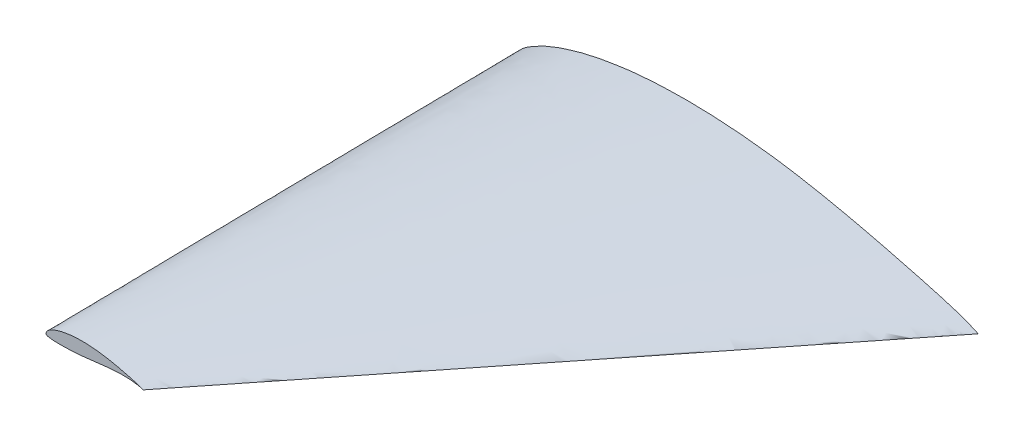
SolidWorks part; units mm, degrees
ref_plane "Front Plane" through (0, 0, 0) normal (0, 0, 1) x (1, 0, 0)
ref_plane "Top Plane" through (0, 0, 0) normal (0, 1, 0) x (1, 0, 0)
ref_plane "Right Plane" through (0, 0, 0) normal (1, 0, 0) x (0, 0, -1)
curve "Curve1"
  spline degree 3 poles (25.3433, 0.0232, 0) (25.4148, -0.0081, 0) (25.3447, 0.0413, 0) (25.2813, 0.0657, 0) (25.1364, 0.1389, 0) (24.9522, 0.2143, 0) (24.7099, 0.3099, 0) (24.4182, 0.4134, 0) (24.075, 0.5249, 0) (23.6837, 0.6446, 0) (23.2451, 0.7712, 0) (22.762, 0.9075, 0) (22.2348, 1.0483, 0) (21.6683, 1.2014, 0) (21.0618, 1.3547, 0) (20.4213, 1.5189, 0) (19.7455, 1.6791, 0) (19.0423, 1.8522, 0) (18.309, 2.0141, 0) (17.5552, 2.1876, 0) (16.7767, 2.3381, 0) (15.9845, 2.4962, 0) (15.1746, 2.6242, 0) (14.3573, 2.7555, 0) (13.5297, 2.8496, 0) (12.7014, 2.9475, 0) (11.8708, 3.0047, 0) (11.0455, 3.0663, 0) (10.2259, 3.0812, 0) (9.4176, 3.1048, 0) (8.6235, 3.079, 0) (7.8457, 3.0638, 0) (7.0909, 2.9938, 0) (6.3564, 2.9377, 0) (5.6543, 2.8235, 0) (4.9756, 2.731, 0) (4.3385, 2.581, 0) (3.7264, 2.4576, 0) (3.1656, 2.2763, 0) (2.6301, 2.1267, 0) (2.1563, 1.9205, 0) (1.705, 1.7526, 0) (1.3258, 1.5314, 0) (0.9764, 1.3443, 0) (0.6751, 1.1512, 0) (0.4363, 0.9319, 0) (0.2358, 0.7054, 0) (0.1108, 0.4617, 0) (0.0257, 0.2336, 0) (-0.0273, 0.0509, 0) (0.0322, -0.0775, 0) (0.1239, -0.1549, 0) (0.243, -0.2723, 0) (0.4522, -0.3184, 0) (0.6848, -0.4066, 0) (0.9848, -0.4273, 0) (1.3238, -0.4905, 0) (1.7178, -0.5018, 0) (2.1546, -0.5475, 0) (2.639, -0.5497, 0) (3.165, -0.58, 0) (3.7327, -0.5712, 0) (4.3384, -0.5844, 0) (4.9797, -0.5607, 0) (5.6547, -0.5539, 0) (6.359, -0.5141, 0) (7.0916, -0.4857, 0) (7.8469, -0.4269, 0) (8.6243, -0.3745, 0) (9.4178, -0.2956, 0) (10.2265, -0.2175, 0) (11.0449, -0.1232, 0) (11.8711, -0.0277, 0) (12.6999, 0.0784, 0) (13.5293, 0.1818, 0) (14.3548, 0.284, 0) (15.1739, 0.3743, 0) (15.9817, 0.4628, 0) (16.7762, 0.5329, 0) (17.5525, 0.5982, 0) (18.3087, 0.6433, 0) (19.0406, 0.6802, 0) (19.7456, 0.6989, 0) (20.4203, 0.7059, 0) (21.0619, 0.6961, 0) (21.6678, 0.6717, 0) (22.2353, 0.633, 0) (22.762, 0.5841, 0) (23.2454, 0.5251, 0) (23.6839, 0.4603, 0) (24.0753, 0.3899, 0) (24.4181, 0.3151, 0) (24.7102, 0.241, 0) (24.9522, 0.1659, 0) (25.1359, 0.1036, 0) (25.2809, 0.0467, 0) (25.3433, 0.0232, 0) (25.4148, -0.0081, 0) (25.3447, 0.0413, 0) knots -0.004989 -0.002227 -0.000553 0 0.000652 0.002403 0.005257 0.009166 0.014097 0.020022 0.026896 0.034706 0.043414 0.05299 0.063397 0.074601 0.086531 0.099154 0.112393 0.126224 0.140545 0.155319 0.170432 0.185859 0.201487 0.217293 0.233167 0.249086 0.264959 0.280748 0.296381 0.311801 0.326956 0.341783 0.356248 0.370275 0.383862 0.396888 0.409401 0.421253 0.432541 0.443065 0.452987 0.462044 0.470526 0.478016 0.48472 0.490901 0.496493 0.501935 0.506332 0.510718 0.511954 0.514196 0.517507 0.521315 0.526107 0.531741 0.538338 0.545822 0.554208 0.563431 0.573484 0.58431 0.595867 0.608108 0.620979 0.634442 0.648424 0.66288 0.677739 0.692957 0.708452 0.724177 0.740042 0.75599 0.771938 0.787811 0.803536 0.81904 0.834255 0.849121 0.86357 0.877552 0.891006 0.903874 0.916114 0.92768 0.938531 0.948622 0.957909 0.966364 0.973953 0.98064 0.986403 0.991207 0.995011 0.997773 0.999447 1 1.000652 1.002403 1.005257 periodic
sketch "Sketch2" plane through (0, 0, 0) normal (0, 0, 1) x (1, 0, 0)
  spline S1 degree 3 poles (608.239, 0.556) (609.9546, -0.1936) (608.2736, 0.9916) (606.7506, 1.5776) (603.2739, 3.334) (598.8535, 5.1438) (593.0379, 7.4365) (586.0369, 9.9205) (577.8011, 12.5987) (568.4098, 15.4715) (557.8817, 18.5085) (546.2874, 21.7798) (533.6356, 25.1594) (520.0396, 28.8341) (505.4823, 32.5117) (490.1111, 36.4547) (473.8932, 40.2989) (457.0161, 44.4518) (439.4155, 48.3382) (421.3244, 52.5025) (402.6417, 56.1139) (383.6287, 59.9093) (364.1912, 62.9812) (344.5751, 66.1328) (324.7138, 68.3905) (304.8343, 70.7403) (284.9, 72.1124) (265.0915, 73.5901) (245.4223, 73.9499) (226.0224, 74.5141) (206.9647, 73.8952) (188.2978, 73.5307) (170.1811, 71.8513) (152.5538, 70.5049) (135.704, 67.7633) (119.414, 65.5429) (104.124, 61.9451) (89.4335, 58.9829) (75.9752, 54.6308) (63.1215, 51.0399) (51.7509, 46.0911) (40.9204, 42.0631) (31.8194, 36.7527) (23.4327, 32.2641) (16.2024, 27.6289) (10.4708, 22.3666) (5.6595, 16.9298) (2.6587, 11.0814) (0.6179, 5.6066) (-0.6559, 1.2222) (0.7722, -1.8604) (2.9726, -3.7182) (5.8311, -6.5355) (10.852, -7.6418) (16.4351, -9.7577) (23.6352, -10.2554) (31.7722, -11.772) (41.2274, -12.0423) (51.7107, -13.1391) (63.337, -13.193) (75.9597, -13.9196) (89.5837, -13.7085) (104.1218, -14.0254) (119.5128, -13.4557) (135.7116, -13.2937) (152.6159, -12.3377) (170.1982, -11.6563) (188.3259, -10.2462) (206.9836, -8.9877) (226.0268, -7.0934) (245.4353, -5.2192) (265.0768, -2.9575) (284.9055, -0.6639) (304.7985, 1.8822) (324.7022, 4.3641) (344.5156, 6.8149) (364.1743, 8.984) (383.5605, 11.108) (402.628, 12.7894) (421.2607, 14.3574) (439.4098, 15.4398) (456.9755, 16.3238) (473.8942, 16.7737) (490.0863, 16.9423) (505.4856, 16.7062) (520.0277, 16.1203) (533.6471, 15.1914) (546.2869, 14.0175) (557.889, 12.6028) (568.4127, 11.0467) (577.8073, 9.3582) (586.0347, 7.5624) (593.0439, 5.783) (598.8529, 3.9824) (603.261, 2.4867) (606.7417, 1.1197) (608.239, 0.556) (609.9546, -0.1936) (608.2736, 0.9916) knots -0.004989 -0.002227 -0.000553 0 0.000652 0.002403 0.005257 0.009166 0.014097 0.020022 0.026896 0.034706 0.043414 0.05299 0.063397 0.074601 0.086531 0.099154 0.112393 0.126224 0.140545 0.155319 0.170432 0.185859 0.201487 0.217293 0.233167 0.249086 0.264959 0.280748 0.296381 0.311801 0.326956 0.341783 0.356248 0.370275 0.383862 0.396888 0.409401 0.421253 0.432541 0.443065 0.452987 0.462044 0.470526 0.478016 0.48472 0.490901 0.496493 0.501935 0.506332 0.510718 0.511954 0.514196 0.517507 0.521315 0.526107 0.531741 0.538338 0.545822 0.554208 0.563431 0.573484 0.58431 0.595867 0.608108 0.620979 0.634442 0.648424 0.66288 0.677739 0.692957 0.708452 0.724177 0.740042 0.75599 0.771938 0.787811 0.803536 0.81904 0.834255 0.849121 0.86357 0.877552 0.891006 0.903874 0.916114 0.92768 0.938531 0.948622 0.957909 0.966364 0.973953 0.98064 0.986403 0.991207 0.995011 0.997773 0.999447 1 1.000652 1.002403 1.005257 only from (609.6, 0) to (609.6, 0)
ref_plane "Plane1" through (0, 0, 609.6) normal (0, 0, 1) x (1, 0, 0)
sketch "Sketch3" plane through (0, 0, 609.6) normal (0, 0, 1) x (1, 0, 0)
  spline S1 degree 3 poles (608.239, 0.556) (609.9546, -0.1936) (608.2736, 0.9916) (606.7506, 1.5776) (603.2739, 3.334) (598.8535, 5.1438) (593.0379, 7.4365) (586.0369, 9.9205) (577.8011, 12.5987) (568.4098, 15.4715) (557.8817, 18.5085) (546.2874, 21.7798) (533.6356, 25.1594) (520.0396, 28.8341) (505.4823, 32.5117) (490.1111, 36.4547) (473.8932, 40.2989) (457.0161, 44.4518) (439.4155, 48.3382) (421.3244, 52.5025) (402.6417, 56.1139) (383.6287, 59.9093) (364.1912, 62.9812) (344.5751, 66.1328) (324.7138, 68.3905) (304.8343, 70.7403) (284.9, 72.1124) (265.0915, 73.5901) (245.4223, 73.9499) (226.0224, 74.5141) (206.9647, 73.8952) (188.2978, 73.5307) (170.1811, 71.8513) (152.5538, 70.5049) (135.704, 67.7633) (119.414, 65.5429) (104.124, 61.9451) (89.4335, 58.9829) (75.9752, 54.6308) (63.1215, 51.0399) (51.7509, 46.0911) (40.9204, 42.0631) (31.8194, 36.7527) (23.4327, 32.2641) (16.2024, 27.6289) (10.4708, 22.3666) (5.6595, 16.9298) (2.6587, 11.0814) (0.6179, 5.6066) (-0.6559, 1.2222) (0.7722, -1.8604) (2.9726, -3.7182) (5.8311, -6.5355) (10.852, -7.6418) (16.4351, -9.7577) (23.6352, -10.2554) (31.7722, -11.772) (41.2274, -12.0423) (51.7107, -13.1391) (63.337, -13.193) (75.9597, -13.9196) (89.5837, -13.7085) (104.1218, -14.0254) (119.5128, -13.4557) (135.7116, -13.2937) (152.6159, -12.3377) (170.1982, -11.6563) (188.3259, -10.2462) (206.9836, -8.9877) (226.0268, -7.0934) (245.4353, -5.2192) (265.0768, -2.9575) (284.9055, -0.6639) (304.7985, 1.8822) (324.7022, 4.3641) (344.5156, 6.8149) (364.1743, 8.984) (383.5605, 11.108) (402.628, 12.7894) (421.2607, 14.3574) (439.4098, 15.4398) (456.9755, 16.3238) (473.8942, 16.7737) (490.0863, 16.9423) (505.4856, 16.7062) (520.0277, 16.1203) (533.6471, 15.1914) (546.2869, 14.0175) (557.889, 12.6028) (568.4127, 11.0467) (577.8073, 9.3582) (586.0347, 7.5624) (593.0439, 5.783) (598.8529, 3.9824) (603.261, 2.4867) (606.7417, 1.1197) (608.239, 0.556) (609.9546, -0.1936) (608.2736, 0.9916) knots -0.004989 -0.002227 -0.000553 0 0.000652 0.002403 0.005257 0.009166 0.014097 0.020022 0.026896 0.034706 0.043414 0.05299 0.063397 0.074601 0.086531 0.099154 0.112393 0.126224 0.140545 0.155319 0.170432 0.185859 0.201487 0.217293 0.233167 0.249086 0.264959 0.280748 0.296381 0.311801 0.326956 0.341783 0.356248 0.370275 0.383862 0.396888 0.409401 0.421253 0.432541 0.443065 0.452987 0.462044 0.470526 0.478016 0.48472 0.490901 0.496493 0.501935 0.506332 0.510718 0.511954 0.514196 0.517507 0.521315 0.526107 0.531741 0.538338 0.545822 0.554208 0.563431 0.573484 0.58431 0.595867 0.608108 0.620979 0.634442 0.648424 0.66288 0.677739 0.692957 0.708452 0.724177 0.740042 0.75599 0.771938 0.787811 0.803536 0.81904 0.834255 0.849121 0.86357 0.877552 0.891006 0.903874 0.916114 0.92768 0.938531 0.948622 0.957909 0.966364 0.973953 0.98064 0.986403 0.991207 0.995011 0.997773 0.999447 1 1.000652 1.002403 1.005257 only from (609.6, 0) to (609.6, 0)
  spline S2 degree 3 poles (608.239, 0.556) (609.9546, -0.1936) (608.2736, 0.9916) (606.7506, 1.5776) (603.2739, 3.334) (598.8535, 5.1438) (593.0379, 7.4365) (586.0369, 9.9205) (577.8011, 12.5987) (568.4098, 15.4715) (557.8817, 18.5085) (546.2874, 21.7798) (533.6356, 25.1594) (520.0396, 28.8341) (505.4823, 32.5117) (490.1111, 36.4547) (473.8932, 40.2989) (457.0161, 44.4518) (439.4155, 48.3382) (421.3244, 52.5025) (402.6417, 56.1139) (383.6287, 59.9093) (364.1912, 62.9812) (344.5751, 66.1328) (324.7138, 68.3905) (304.8343, 70.7403) (284.9, 72.1124) (265.0915, 73.5901) (245.4223, 73.9499) (226.0224, 74.5141) (206.9647, 73.8952) (188.2978, 73.5307) (170.1811, 71.8513) (152.5538, 70.5049) (135.704, 67.7633) (119.414, 65.5429) (104.124, 61.9451) (89.4335, 58.9829) (75.9752, 54.6308) (63.1215, 51.0399) (51.7509, 46.0911) (40.9204, 42.0631) (31.8194, 36.7527) (23.4327, 32.2641) (16.2024, 27.6289) (10.4708, 22.3666) (5.6595, 16.9298) (2.6587, 11.0814) (0.6179, 5.6066) (-0.6559, 1.2222) (0.7722, -1.8604) (2.9726, -3.7182) (5.8311, -6.5355) (10.852, -7.6418) (16.4351, -9.7577) (23.6352, -10.2554) (31.7722, -11.772) (41.2274, -12.0423) (51.7107, -13.1391) (63.337, -13.193) (75.9597, -13.9196) (89.5837, -13.7085) (104.1218, -14.0254) (119.5128, -13.4557) (135.7116, -13.2937) (152.6159, -12.3377) (170.1982, -11.6563) (188.3259, -10.2462) (206.9836, -8.9877) (226.0268, -7.0934) (245.4353, -5.2192) (265.0768, -2.9575) (284.9055, -0.6639) (304.7985, 1.8822) (324.7022, 4.3641) (344.5156, 6.8149) (364.1743, 8.984) (383.5605, 11.108) (402.628, 12.7894) (421.2607, 14.3574) (439.4098, 15.4398) (456.9755, 16.3238) (473.8942, 16.7737) (490.0863, 16.9423) (505.4856, 16.7062) (520.0277, 16.1203) (533.6471, 15.1914) (546.2869, 14.0175) (557.889, 12.6028) (568.4127, 11.0467) (577.8073, 9.3582) (586.0347, 7.5624) (593.0439, 5.783) (598.8529, 3.9824) (603.261, 2.4867) (606.7417, 1.1197) (608.239, 0.556) (609.9546, -0.1936) (608.2736, 0.9916) knots -0.004989 -0.002227 -0.000553 0 0.000652 0.002403 0.005257 0.009166 0.014097 0.020022 0.026896 0.034706 0.043414 0.05299 0.063397 0.074601 0.086531 0.099154 0.112393 0.126224 0.140545 0.155319 0.170432 0.185859 0.201487 0.217293 0.233167 0.249086 0.264959 0.280748 0.296381 0.311801 0.326956 0.341783 0.356248 0.370275 0.383862 0.396888 0.409401 0.421253 0.432541 0.443065 0.452987 0.462044 0.470526 0.478016 0.48472 0.490901 0.496493 0.501935 0.506332 0.510718 0.511954 0.514196 0.517507 0.521315 0.526107 0.531741 0.538338 0.545822 0.554208 0.563431 0.573484 0.58431 0.595867 0.608108 0.620979 0.634442 0.648424 0.66288 0.677739 0.692957 0.708452 0.724177 0.740042 0.75599 0.771938 0.787811 0.803536 0.81904 0.834255 0.849121 0.86357 0.877552 0.891006 0.903874 0.916114 0.92768 0.938531 0.948622 0.957909 0.966364 0.973953 0.98064 0.986403 0.991207 0.995011 0.997773 0.999447 1 1.000652 1.002403 1.005257 only from (609.6, 0) to (609.6, 0)
  spline S3 degree 3 poles (126.7165, 0.1158) (127.0739, -0.0403) (126.7237, 0.2066) (126.4064, 0.3287) (125.6821, 0.6946) (124.7612, 1.0716) (123.5496, 1.5493) (122.091, 2.0668) (120.3752, 2.6247) (118.4187, 3.2232) (116.2253, 3.8559) (113.8099, 4.5375) (111.1741, 5.2415) (108.3416, 6.0071) (105.3088, 6.7733) (102.1065, 7.5947) (98.7277, 8.3956) (95.2117, 9.2608) (91.5449, 10.0705) (87.7759, 10.938) (83.8837, 11.6904) (79.9227, 12.4811) (75.8732, 13.1211) (71.7865, 13.7777) (67.6487, 14.248) (63.5071, 14.7376) (59.3542, 15.0234) (55.2274, 15.3313) (51.1296, 15.4062) (47.088, 15.5238) (43.1177, 15.3948) (39.2287, 15.3189) (35.4544, 14.969) (31.782, 14.6885) (28.2717, 14.1173) (24.8779, 13.6548) (21.6925, 12.9052) (18.632, 12.2881) (15.8282, 11.3814) (13.1503, 10.6333) (10.7814, 9.6023) (8.5251, 8.7631) (6.629, 7.6568) (4.8818, 6.7217) (3.3755, 5.756) (2.1814, 4.6597) (1.1791, 3.527) (0.5539, 2.3086) (0.1287, 1.168) (-0.1367, 0.2546) (0.1609, -0.3876) (0.6193, -0.7746) (1.2148, -1.3616) (2.2608, -1.592) (3.424, -2.0328) (4.924, -2.1365) (6.6192, -2.4525) (8.589, -2.5088) (10.7731, -2.7373) (13.1952, -2.7485) (15.8249, -2.8999) (18.6633, -2.8559) (21.692, -2.922) (24.8985, -2.8033) (28.2733, -2.7695) (31.795, -2.5704) (35.4579, -2.4284) (39.2346, -2.1346) (43.1216, -1.8724) (47.0889, -1.4778) (51.1324, -1.0873) (55.2243, -0.6162) (59.3553, -0.1383) (63.4997, 0.3921) (67.6463, 0.9092) (71.7741, 1.4198) (75.8696, 1.8717) (79.9084, 2.3142) (83.8808, 2.6645) (87.7627, 2.9911) (91.5437, 3.2166) (95.2032, 3.4008) (98.728, 3.4945) (102.1013, 3.5296) (105.3095, 3.4805) (108.3391, 3.3584) (111.1765, 3.1649) (113.8098, 2.9203) (116.2269, 2.6256) (118.4193, 2.3014) (120.3765, 1.9496) (122.0906, 1.5755) (123.5508, 1.2048) (124.761, 0.8297) (125.6794, 0.5181) (126.4045, 0.2333) (126.7165, 0.1158) (127.0739, -0.0403) (126.7237, 0.2066) knots -0.004989 -0.002227 -0.000553 0 0.000652 0.002403 0.005257 0.009166 0.014097 0.020022 0.026896 0.034706 0.043414 0.05299 0.063397 0.074601 0.086531 0.099154 0.112393 0.126224 0.140545 0.155319 0.170432 0.185859 0.201487 0.217293 0.233167 0.249086 0.264959 0.280748 0.296381 0.311801 0.326956 0.341783 0.356248 0.370275 0.383862 0.396888 0.409401 0.421253 0.432541 0.443065 0.452987 0.462044 0.470526 0.478016 0.48472 0.490901 0.496493 0.501935 0.506332 0.510718 0.511954 0.514196 0.517507 0.521315 0.526107 0.531741 0.538338 0.545822 0.554208 0.563431 0.573484 0.58431 0.595867 0.608108 0.620979 0.634442 0.648424 0.66288 0.677739 0.692957 0.708452 0.724177 0.740042 0.75599 0.771938 0.787811 0.803536 0.81904 0.834255 0.849121 0.86357 0.877552 0.891006 0.903874 0.916114 0.92768 0.938531 0.948622 0.957909 0.966364 0.973953 0.98064 0.986403 0.991207 0.995011 0.997773 0.999447 1 1.000652 1.002403 1.005257 only from (127, 0) to (127, 0)
  dimension "D1" = 0
loft "Loft3" add profiles "Sketch2" section "Sketch3" section "Sketch2"
